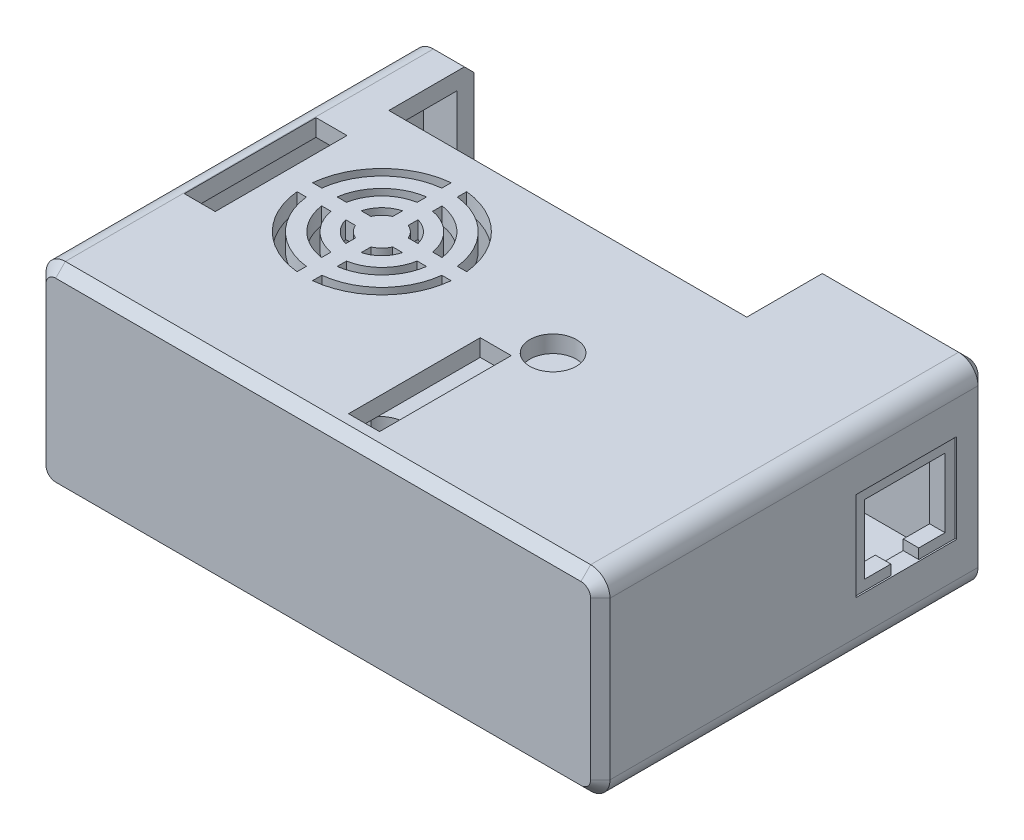
SolidWorks part; units mm, degrees
material "ABS"
ref_plane "Front" through (0, 0, 0) normal (0, 0, 1) x (1, 0, 0)
ref_plane "Top" through (0, 0, 0) normal (0, 1, 0) x (1, 0, 0)
ref_plane "Section" through (0, 0, 0) normal (1, 0, 0) x (0, 0, -1)
sketch "Sketch1" plane through (0, 0, 0) normal (0, 1, 0) x (1, 0, 0)
  line L1 (46.228, -31.75) -> (-46.228, -31.75)
  line L2 (46.228, -31.75) -> (46.228, 31.75)
  line L3 (46.228, 31.75) -> (-46.228, 31.75)
  line L4 (-46.228, -31.75) -> (-46.228, 31.75)
  line L5 (46.228, -31.75) -> (-46.228, 31.75) construction
  line L6 (46.228, 31.75) -> (-46.228, -31.75) construction
  point P0 (0, 0)
  dimension "D1" = 63.5
  dimension "D2" = 92.456
extrude "Boss-Extrude1" add sketch "Sketch1" against normal blind 32.131
fillet "Fillet1" radius 3.175 4 edges at (-46.228, 0, 0) (-46.228, -32.131, 0) (46.228, -32.131, 0) (46.228, 0, 0)
chamfer "Chamfer1" distance 1.5875 angle 45 16 edges at (0, -32.131, -31.75) (45.2981, -31.2011, -31.75) (-45.2981, -31.2011, -31.75) (46.228, -16.0655, -31.75) (-46.228, -16.0655, -31.75) (45.2981, -0.9299, -31.75) (-45.2981, -0.9299, -31.75) (0, 0, -31.75) (0, -32.131, 31.75) (-45.2981, -31.2011, 31.75) (45.2981, -31.2011, 31.75) (-46.228, -16.0655, 31.75) (46.228, -16.0655, 31.75) (-45.2981, -0.9299, 31.75) (45.2981, -0.9299, 31.75) (0, 0, 31.75)
shell "Shell1" thickness 2.794
sketch "Sketch2" plane through (0, 0, 0) normal (0, 1, 0) x (1, 0, 0)
  line L0 (-43.053, 31.75) -> (43.053, 31.75) construction
  line L1 (-37.973, 31.75) -> (20.701, 31.75)
  line L2 (-37.973, 31.75) -> (-37.973, 17.78)
  line L3 (-37.973, 17.78) -> (20.701, 17.78)
  line L4 (20.701, 31.75) -> (20.701, 17.78)
  line L5 (-46.228, -30.1625) -> (-46.228, 30.1625) construction
  dimension "D1" = 58.674
  dimension "D2" = 8.255
  dimension "D3" = 13.97
extrude "Cut-Extrude1" cut sketch "Sketch2" against normal blind 15.24
sketch "Sketch3" plane through (0, -32.131, 0) normal (0, -1, 0) x (1, 0, 0)
  line L1 (36.83, -22.86) -> (-36.83, -22.86) construction
  line L2 (36.83, -22.86) -> (36.83, 22.86) construction
  line L3 (36.83, 22.86) -> (-36.83, 22.86) construction
  line L4 (-36.83, -22.86) -> (-36.83, 22.86) construction
  line L5 (36.83, -22.86) -> (-36.83, 22.86) construction
  line L6 (36.83, 22.86) -> (-36.83, -22.86) construction
  circle A0 centre (-36.83, 22.86) radius 3.4925
  circle A1 centre (36.83, -22.86) radius 3.4925
  circle A2 centre (36.83, 22.86) radius 3.4925
  circle A3 centre (-36.83, -22.86) radius 3.4925
  circle A4 centre (-36.83, 22.86) radius 2.3495
  circle A5 centre (36.83, 22.86) radius 2.3495
  circle A6 centre (-36.83, -22.86) radius 2.3495
  circle A7 centre (36.83, -22.86) radius 2.3495
  point P8 (0, 0)
  dimension "D3" = 6.985
  dimension "D4" = 1.143
  dimension "D1" = 73.66
  dimension "D2" = 45.72
extrude "Boss-Extrude2" add sketch "Sketch3" along normal blind 1.143
sketch "Sketch4" plane through (0, -32.131, 0) normal (0, -1, 0) x (1, 0, 0)
  line L0 (-43.053, 0) -> (43.053, 0) construction
  line L1 (-43.053, 30.1625) -> (-43.053, -30.1625) construction
  line L2 (43.053, -30.1625) -> (43.053, 30.1625) construction
  line L3 (0, 30.1625) -> (0, -30.1625) construction
  line L4 (43.053, 30.1625) -> (-43.053, 30.1625) construction
  line L5 (-43.053, -30.1625) -> (43.053, -30.1625) construction
  line L6 (-11.8745, 12.954) -> (-11.8745, 3.556) construction
  line L7 (-10.6045, 12.954) -> (-10.6045, 3.556)
  line L8 (-13.1445, 12.954) -> (-13.1445, 3.556)
  line L9 (-43.053, 31.75) -> (43.053, 31.75) construction
  line L10 (-7.1247, 12.954) -> (-7.1247, 3.556) construction
  line L11 (-5.8547, 12.954) -> (-5.8547, 3.556)
  line L12 (-8.3947, 12.954) -> (-8.3947, 3.556)
  line L13 (-2.3749, 12.954) -> (-2.3749, 3.556) construction
  line L14 (-1.1049, 12.954) -> (-1.1049, 3.556)
  line L15 (-3.6449, 12.954) -> (-3.6449, 3.556)
  line L16 (2.3749, 12.954) -> (2.3749, 3.556) construction
  line L17 (3.6449, 12.954) -> (3.6449, 3.556)
  line L18 (1.1049, 12.954) -> (1.1049, 3.556)
  line L19 (7.1247, 12.954) -> (7.1247, 3.556) construction
  line L20 (8.3947, 12.954) -> (8.3947, 3.556)
  line L21 (5.8547, 12.954) -> (5.8547, 3.556)
  line L22 (11.8745, 12.954) -> (11.8745, 3.556) construction
  line L23 (13.1445, 12.954) -> (13.1445, 3.556)
  line L24 (10.6045, 12.954) -> (10.6045, 3.556)
  line L25 (-11.8745, -12.954) -> (-11.8745, -3.556) construction
  line L26 (-10.6045, -12.954) -> (-10.6045, -3.556)
  line L27 (-13.1445, -12.954) -> (-13.1445, -3.556)
  line L28 (-7.1247, -12.954) -> (-7.1247, -3.556) construction
  line L29 (-5.8547, -12.954) -> (-5.8547, -3.556)
  line L30 (-8.3947, -12.954) -> (-8.3947, -3.556)
  line L31 (-2.3749, -12.954) -> (-2.3749, -3.556) construction
  line L32 (-1.1049, -12.954) -> (-1.1049, -3.556)
  line L33 (-3.6449, -12.954) -> (-3.6449, -3.556)
  line L34 (2.3749, -12.954) -> (2.3749, -3.556) construction
  line L35 (3.6449, -12.954) -> (3.6449, -3.556)
  line L36 (1.1049, -12.954) -> (1.1049, -3.556)
  line L37 (7.1247, -12.954) -> (7.1247, -3.556) construction
  line L38 (8.3947, -12.954) -> (8.3947, -3.556)
  line L39 (5.8547, -12.954) -> (5.8547, -3.556)
  line L40 (11.8745, -12.954) -> (11.8745, -3.556) construction
  line L41 (13.1445, -12.954) -> (13.1445, -3.556)
  line L42 (10.6045, -12.954) -> (10.6045, -3.556)
  line L43 (16.383, 0) -> (27.051, 0) construction
  line L44 (16.383, 2.159) -> (18.1992, 2.159)
  line L45 (16.383, -2.159) -> (18.1992, -2.159)
  line L46 (46.228, 30.1625) -> (46.228, -30.1625) construction
  line L47 (25.2348, 2.159) -> (27.051, 2.159)
  line L48 (25.2348, -2.159) -> (27.051, -2.159)
  line L49 (-16.383, 2.159) -> (-18.1992, 2.159)
  line L50 (-25.2348, 2.159) -> (-27.051, 2.159)
  line L51 (-25.2348, -2.159) -> (-27.051, -2.159)
  line L52 (-16.383, -2.159) -> (-18.1992, -2.159)
  arc A0 (-10.6045, 12.954) -> (-13.1445, 12.954) centre (-11.8745, 12.954) ccw
  arc A1 (-13.1445, 3.556) -> (-10.6045, 3.556) centre (-11.8745, 3.556) ccw
  arc A2 (-5.8547, 12.954) -> (-8.3947, 12.954) centre (-7.1247, 12.954) ccw
  arc A3 (-8.3947, 3.556) -> (-5.8547, 3.556) centre (-7.1247, 3.556) ccw
  arc A4 (-1.1049, 12.954) -> (-3.6449, 12.954) centre (-2.3749, 12.954) ccw
  arc A5 (-3.6449, 3.556) -> (-1.1049, 3.556) centre (-2.3749, 3.556) ccw
  arc A6 (3.6449, 12.954) -> (1.1049, 12.954) centre (2.3749, 12.954) ccw
  arc A7 (1.1049, 3.556) -> (3.6449, 3.556) centre (2.3749, 3.556) ccw
  arc A8 (8.3947, 12.954) -> (5.8547, 12.954) centre (7.1247, 12.954) ccw
  arc A9 (5.8547, 3.556) -> (8.3947, 3.556) centre (7.1247, 3.556) ccw
  arc A10 (13.1445, 12.954) -> (10.6045, 12.954) centre (11.8745, 12.954) ccw
  arc A11 (10.6045, 3.556) -> (13.1445, 3.556) centre (11.8745, 3.556) ccw
  arc A12 (-10.6045, -12.954) -> (-13.1445, -12.954) centre (-11.8745, -12.954) cw
  arc A13 (-13.1445, -3.556) -> (-10.6045, -3.556) centre (-11.8745, -3.556) cw
  arc A14 (-5.8547, -12.954) -> (-8.3947, -12.954) centre (-7.1247, -12.954) cw
  arc A15 (-8.3947, -3.556) -> (-5.8547, -3.556) centre (-7.1247, -3.556) cw
  arc A16 (-1.1049, -12.954) -> (-3.6449, -12.954) centre (-2.3749, -12.954) cw
  arc A17 (-3.6449, -3.556) -> (-1.1049, -3.556) centre (-2.3749, -3.556) cw
  arc A18 (3.6449, -12.954) -> (1.1049, -12.954) centre (2.3749, -12.954) cw
  arc A19 (1.1049, -3.556) -> (3.6449, -3.556) centre (2.3749, -3.556) cw
  arc A20 (8.3947, -12.954) -> (5.8547, -12.954) centre (7.1247, -12.954) cw
  arc A21 (5.8547, -3.556) -> (8.3947, -3.556) centre (7.1247, -3.556) cw
  arc A22 (13.1445, -12.954) -> (10.6045, -12.954) centre (11.8745, -12.954) cw
  arc A23 (10.6045, -3.556) -> (13.1445, -3.556) centre (11.8745, -3.556) cw
  arc A24 (16.383, 2.159) -> (16.383, -2.159) centre (16.383, 0) ccw
  arc A25 (27.051, -2.159) -> (27.051, 2.159) centre (27.051, 0) ccw
  arc A26 (18.1992, -2.159) -> (25.2348, -2.159) centre (21.717, 0) ccw
  arc A27 (25.2348, 2.159) -> (18.1992, 2.159) centre (21.717, 0) ccw
  arc A28 (-25.2348, 2.159) -> (-18.1992, 2.159) centre (-21.717, 0) cw
  arc A29 (-27.051, -2.159) -> (-27.051, 2.159) centre (-27.051, 0) cw
  arc A30 (-18.1992, -2.159) -> (-25.2348, -2.159) centre (-21.717, 0) cw
  arc A31 (-16.383, 2.159) -> (-16.383, -2.159) centre (-16.383, 0) cw
  point P14 (-11.8745, 8.255)
  point P24 (-7.1247, 8.255)
  point P30 (-2.3749, 8.255)
  point P37 (2.3749, 8.255)
  point P44 (7.1247, 8.255)
  point P51 (11.8745, 8.255)
  point P58 (-11.8745, -8.255)
  point P65 (-7.1247, -8.255)
  point P72 (-2.3749, -8.255)
  point P79 (2.3749, -8.255)
  point P86 (7.1247, -8.255)
  point P93 (11.8745, -8.255)
  point P100 (21.717, 0)
  point P111 (27.051, 0)
  point P113 (0, 0)
  point P114 (0, 0)
  point P115 (0, 0)
  dimension "D2" = 11.938
  dimension "D8" = 14.986
  dimension "D10" = 8.255
  dimension "D1" = 2.54
  dimension "D3" = 17.526
  dimension "D5" = 13.1445
  dimension "D6" = 2.2098
  dimension "D7" = 4.318
  dimension "D9" = 17.018
  dimension "D4" = 6
extrude "Cut-Extrude2" cut sketch "Sketch4" against normal blind 3.175
sketch "Sketch5" plane through (0, -32.131, 0) normal (0, -1, 0) x (1, 0, 0)
  line L0 (-46.228, -30.1625) -> (-46.228, 30.1625) construction
  line L1 (-46.228, 7.239) -> (-38.608, 7.239)
  line L2 (-46.228, 7.239) -> (-46.228, -7.239)
  line L3 (-46.228, -7.239) -> (-38.608, -7.239)
  line L4 (-38.608, 7.239) -> (-38.608, -7.239)
  line L5 (-38.608, 0) -> (0, 0) construction
  dimension "D1" = 14.478
  dimension "D2" = 7.62
extrude "Cut-Extrude3" cut sketch "Sketch5" against normal blind 7.366
sketch "Sketch6" plane through (0, 0, 0) normal (0, 1, 0) x (1, 0, 0)
  line L0 (-46.228, -30.1625) -> (-46.228, 30.1625) construction
  line L1 (-42.926, 10.795) -> (-37.846, 10.795)
  line L2 (-42.926, 10.795) -> (-42.926, -10.795)
  line L3 (-42.926, -10.795) -> (-37.846, -10.795)
  line L4 (-37.846, 10.795) -> (-37.846, -10.795)
  line L5 (1.778, -6.985) -> (6.858, -6.985)
  line L6 (1.778, -6.985) -> (1.778, -28.575)
  line L7 (1.778, -28.575) -> (6.858, -28.575)
  line L8 (6.858, -6.985) -> (6.858, -28.575)
  line L9 (-37.846, 0) -> (-21.336, 0) construction
  line L10 (-21.336, 0) -> (0, 0) construction
  line L11 (46.228, 30.1625) -> (46.228, -30.1625) construction
  line L12 (43.053, -31.75) -> (-43.053, -31.75) construction
  line L13 (-22.606, 11.1036) -> (-22.606, 12.6363)
  line L15 (-20.066, -12.6363) -> (-20.066, -11.1036)
  line L17 (-22.606, -12.6363) -> (-22.606, -11.1036)
  line L18 (-20.066, -15.4305) -> (-22.606, 15.4305) construction
  line L19 (-20.066, 15.4305) -> (-22.606, -15.4305) construction
  line L20 (-33.9723, 1.27) -> (-32.4396, 1.27)
  line L22 (-33.9723, -1.27) -> (-32.4396, -1.27)
  line L24 (-36.7665, 1.27) -> (-5.9055, -1.27) construction
  line L25 (-36.7665, -1.27) -> (-5.9055, 1.27) construction
  line L26 (-22.606, 3.048) -> (-22.606, 4.6559)
  line L27 (-20.066, 3.048) -> (-20.066, 4.6559)
  line L28 (-20.066, 11.1036) -> (-20.066, 12.6363)
  line L29 (-20.066, 7.0622) -> (-20.066, 8.6063)
  line L30 (-18.288, -1.27) -> (-16.6801, -1.27)
  line L31 (-18.288, 1.27) -> (-16.6801, 1.27)
  line L32 (-22.606, 7.0622) -> (-22.606, 8.6063)
  line L33 (-14.2738, 1.27) -> (-12.7297, 1.27)
  line L34 (-14.2738, -1.27) -> (-12.7297, -1.27)
  line L35 (-10.2324, 1.27) -> (-8.6997, 1.27)
  line L36 (-10.2324, -1.27) -> (-8.6997, -1.27)
  line L37 (-25.9919, -1.27) -> (-24.384, -1.27)
  line L38 (-25.9919, 1.27) -> (-24.384, 1.27)
  line L39 (-29.9423, 1.27) -> (-28.3982, 1.27)
  line L40 (-29.9423, -1.27) -> (-28.3982, -1.27)
  line L41 (-20.066, -4.6559) -> (-20.066, -3.048)
  line L42 (-22.606, -4.6559) -> (-22.606, -3.048)
  line L43 (-20.066, -8.6063) -> (-20.066, -7.0622)
  line L44 (-22.606, -8.6063) -> (-22.606, -7.0622)
  line L45 (-22.606, 15.4305) -> (-20.066, 15.4305) construction
  line L46 (-21.336, 15.4305) -> (-21.336, 0) construction
  line L47 (-5.9055, 1.27) -> (-5.9055, -1.27) construction
  line L48 (-5.9055, 0) -> (-21.336, 0) construction
  circle A0 centre (9.906, -3.175) radius 3.81
  arc A1 (-33.9723, -1.27) -> (-22.606, -12.6363) centre (-21.336, 0) ccw
  arc A2 (-10.2324, 1.27) -> (-20.066, 11.1036) centre (-21.336, 0) ccw
  arc A3 (-12.7297, 1.27) -> (-20.066, 8.6063) centre (-21.336, 0) ccw
  arc A4 (-14.2738, 1.27) -> (-20.066, 7.0622) centre (-21.336, 0) ccw
  arc A5 (-16.6801, 1.27) -> (-20.066, 4.6559) centre (-21.336, 0) ccw
  arc A6 (-22.606, 3.048) -> (-24.384, 1.27) centre (-21.336, 0) ccw
  arc A7 (-18.288, 1.27) -> (-20.066, 3.048) centre (-21.336, 0) ccw
  arc A8 (-25.9919, -1.27) -> (-22.606, -4.6559) centre (-21.336, 0) ccw
  arc A9 (-20.066, -3.048) -> (-18.288, -1.27) centre (-21.336, 0) ccw
  arc A10 (-28.3982, -1.27) -> (-22.606, -7.0622) centre (-21.336, 0) ccw
  arc A11 (-24.384, -1.27) -> (-22.606, -3.048) centre (-21.336, 0) ccw
  arc A12 (-29.9423, -1.27) -> (-22.606, -8.6063) centre (-21.336, 0) ccw
  arc A13 (-32.4396, -1.27) -> (-22.606, -11.1036) centre (-21.336, 0) ccw
  arc A14 (-8.6997, 1.27) -> (-20.066, 12.6363) centre (-21.336, 0) ccw
  arc A15 (-20.066, -4.6559) -> (-16.6801, -1.27) centre (-21.336, 0) ccw
  arc A16 (-20.066, -7.0622) -> (-14.2738, -1.27) centre (-21.336, 0) ccw
  arc A17 (-20.066, -8.6063) -> (-12.7297, -1.27) centre (-21.336, 0) ccw
  arc A18 (-20.066, -11.1036) -> (-10.2324, -1.27) centre (-21.336, 0) ccw
  arc A19 (-20.066, -12.6363) -> (-8.6997, -1.27) centre (-21.336, 0) ccw
  arc A20 (-22.606, 4.6559) -> (-25.9919, 1.27) centre (-21.336, 0) ccw
  arc A21 (-22.606, 7.0622) -> (-28.3982, 1.27) centre (-21.336, 0) ccw
  arc A22 (-22.606, 8.6063) -> (-29.9423, 1.27) centre (-21.336, 0) ccw
  arc A23 (-22.606, 11.1036) -> (-32.4396, 1.27) centre (-21.336, 0) ccw
  arc A24 (-22.606, 12.6363) -> (-33.9723, 1.27) centre (-21.336, 0) ccw
  point P78 (-10.2324, -1.27)
  point P79 (0, 0)
  dimension "D4" = 7.62
  dimension "D10" = 25.4
  dimension "D11" = 6.604
  dimension "D12" = 17.399
  dimension "D13" = 1.524
  dimension "D14" = 1.524
  dimension "D15" = 1.524
  dimension "D1" = 5.08
  dimension "D2" = 21.59
  dimension "D3" = 3.302
  dimension "D5" = 36.322
  dimension "D6" = 28.575
  dimension "D7" = 39.37
  dimension "D8" = 3.175
  dimension "D9" = 3.81
  dimension "D16" = 2.54
  dimension "D17" = 2.54
  dimension "D18" = 1.27
  dimension "D19" = 30.861
  dimension "D20" = 30.861
extrude "Cut-Extrude4" cut sketch "Sketch6" against normal blind 3.175
sketch "Sketch7" plane through (46.228, 0, 0) normal (1, 0, 0) x (0, 0, -1)
  line L0 (31.75, -3.175) -> (31.75, -28.956) construction
  line L1 (10.16, -8.636) -> (26.67, -8.636)
  line L2 (10.16, -8.636) -> (10.16, -23.241)
  line L3 (10.16, -23.241) -> (26.67, -23.241)
  line L4 (26.67, -8.636) -> (26.67, -23.241)
  line L5 (30.1625, -32.131) -> (-30.1625, -32.131) construction
  dimension "D1" = 14.605
  dimension "D2" = 16.51
  dimension "D3" = 5.08
  dimension "D4" = 8.89
extrude "Cut-Extrude5" cut sketch "Sketch7" against normal blind 0.254
sketch "Sketch8" plane through (45.974, 0, 0) normal (1, 0, 0) x (0, 0, -1)
  line L0 (10.16, -23.241) -> (26.67, -23.241) construction
  line L1 (11.811, -10.287) -> (25.019, -10.287)
  line L2 (11.811, -10.287) -> (11.811, -21.59)
  line L3 (11.811, -21.59) -> (16.129, -21.59)
  line L4 (25.019, -10.287) -> (25.019, -21.59)
  line L6 (16.129, -21.59) -> (16.129, -23.241)
  line L7 (16.129, -23.241) -> (20.701, -23.241)
  line L8 (20.701, -21.59) -> (20.701, -23.241)
  line L9 (20.701, -21.59) -> (25.019, -21.59)
  line L10 (18.415, -8.636) -> (18.415, -10.287) construction
  line L11 (26.67, -8.636) -> (10.16, -8.636) construction
  line L12 (18.415, -10.287) -> (18.415, -23.241) construction
  line L13 (26.67, -23.241) -> (26.67, -8.636) construction
  line L14 (20.701, -21.59) -> (16.129, -21.59) construction
  line L15 (26.67, -8.636) -> (10.16, -8.636) construction
  point P14 (18.415, -21.59)
  point P16 (0, 0)
  point P17 (0, 0)
  dimension "D1" = 1.651
  dimension "D2" = 1.651
  dimension "D3" = 1.651
  dimension "D4" = 4.572
extrude "Cut-Extrude6" cut sketch "Sketch8" against normal blind 12.7
